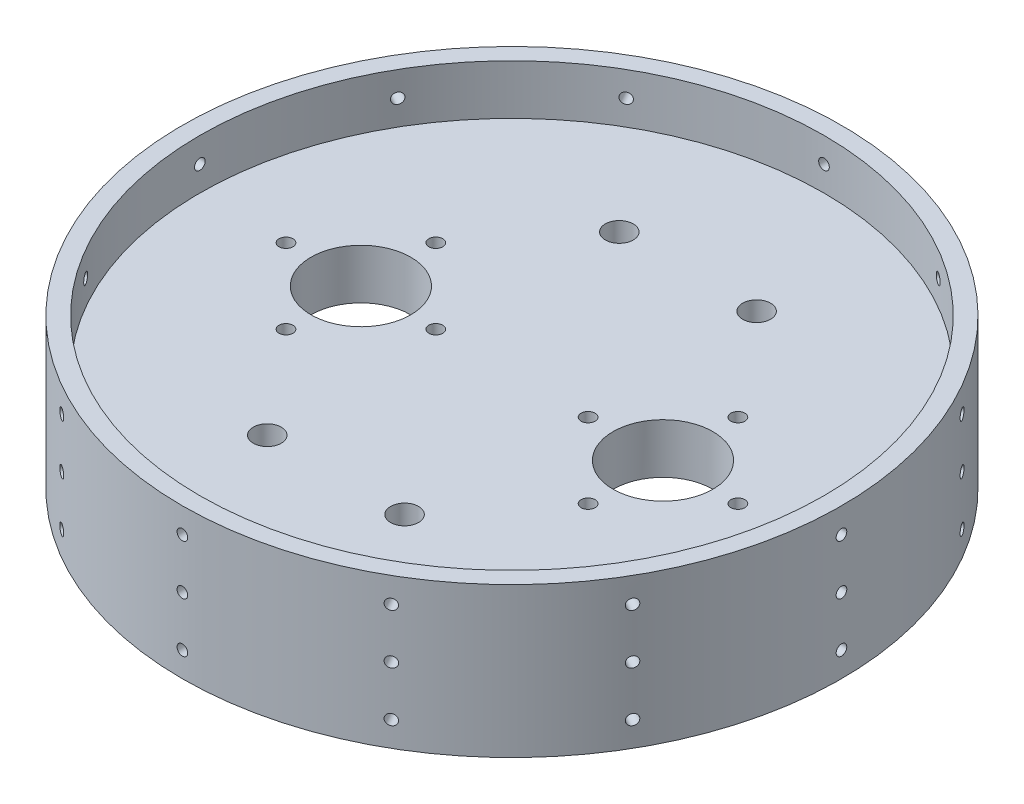
SolidWorks part; units mm, degrees
material "6061-T6 (SS)"
ref_plane "Front" through (0, 0, 0) normal (0, 0, 1) x (1, 0, 0)
ref_plane "Top" through (0, 0, 0) normal (0, 1, 0) x (1, 0, 0)
ref_plane "Right" through (0, 0, 0) normal (1, 0, 0) x (0, 0, -1)
sketch "Sketch1" plane through (0, 0, 0) normal (0, 1, 0) x (1, 0, 0)
  line L1 (0, 0) -> (127.635, 0)
  line L2 (0, 0) -> (0, 127.635)
  line L3 (0, 127.635) -> (127.635, 127.635)
  line L4 (127.635, 0) -> (127.635, 127.635)
  dimension "D1" = 127.635
  dimension "D2" = 127.635
extrude "Main Plate" add sketch "Sketch1" along normal blind 12.7
sketch "Sketch9" plane through (0, 12.7, 0) normal (0, 1, 0) x (1, 0, 0)
  circle A0 centre (63.8175, 63.8175) radius 85.725
  dimension "D1" = 171.45
extrude "Boss-Extrude1" add sketch "Sketch9" against normal up to surface (12.7 mm away) contours A0 up to face at (63.8175, 0, -63.8175)
sketch "Sketch10" plane through (0, 12.7, 0) normal (0, 1, 0) x (1, 0, 0)
  circle A0 centre (63.8175, 63.8175) radius 97.0396
  circle A1 centre (63.8175, 63.8175) radius 83.82
extrude "Cut-Extrude1" cut sketch "Sketch10" against normal blind 167.64 contours A0 | A1
sketch "Sketch14" plane through (0, 12.7, 0) normal (0, 1, 0) x (1, 0, 0)
  line L0 (201.1692, 63.8175) -> (-73.4523, 63.8175) construction
ref_plane "Plane1" through (0, 0, -63.8175) normal (0, 0, -1) x (-1, 0, 0)
ref_plane "Plane3" through (0, 6.35, 0) normal (0, 1, 0) x (1, 0, 0)
ref_plane "Plane2" through (-20.0025, 0, 0) normal (-1, 0, 0) x (0, 0, 1)
sketch "Sketch18" plane through (0, 6.35, 0) normal (0, 1, 0) x (1, 0, 0)
  circle A0 centre (63.8175, 63.8175) radius 83.82
  circle A1 centre (63.8175, 63.8175) radius 79.375
  dimension "D1" = 158.75
extrude "Boss-Extrude2" add sketch "Sketch18" along normal mid plane 38.1
sketch "Sketch15" plane through (-20.0025, 0, 0) normal (-1, 0, 0) x (0, 0, 1)
  line L0 (-63.8175, 92.202) -> (-63.8175, -92.202) construction
  line L1 (20.0025, 12.7) -> (-147.6375, 12.7) construction
  line L2 (-147.6375, -12.7) -> (20.0025, -12.7) construction
  line L3 (15.5575, 25.4) -> (-143.1925, 25.4) construction
  circle A0 centre (-63.8175, 6.35) radius 1.3526
  circle A1 centre (-63.8175, 19.05) radius 1.3525
  circle A2 centre (-63.8175, -6.35) radius 1.3526
  dimension "D1" = 2.7051
  dimension "D2" = 6.35
  dimension "D3" = 2.7051
  dimension "D4" = 2.7051
  dimension "D5" = 6.35
  dimension "D6" = 6.35
extrude "Cut-Extrude3" cut sketch "Sketch15" against normal blind 15.24
pattern_circular "CirPattern1" count 12 over 360 about axis through (63.8175, 0, -63.8175) along (0, 1, 0) of "Cut-Extrude3"
sketch "Sketch20" plane through (0, 12.7, 0) normal (0, 1, 0) x (1, 0, 0)
  line L0 (63.8175, 143.1925) -> (63.8175, -15.5575) construction
  line L1 (-15.5575, 63.8175) -> (143.1925, 63.8175) construction
  circle A0 centre (63.8175, 63.8175) radius 79.375 construction
ref_plane "Plane4" through (63.8175, 0, 0) normal (-1, 0, 0) x (0, 0, 1)
sketch "Sketch21" plane through (0, 12.7, 0) normal (0, 1, 0) x (1, 0, 0)
  line L1 (-15.5575, 63.8175) -> (143.1925, 63.8175) construction
  line L2 (102.235, 63.8175) -> (102.235, 100.651) construction
  line L3 (63.8175, 87.3125) -> (63.8175, -87.3125) construction
  circle A0 centre (102.235, 63.8175) radius 12.7
  circle A1 centre (102.235, 82.8675) radius 1.778
  circle A2 centre (25.4, 63.8175) radius 12.7
  circle A3 centre (121.285, 63.8175) radius 1.778
  circle A4 centre (102.235, 44.7675) radius 1.778
  circle A5 centre (83.185, 63.8175) radius 1.778
  circle A6 centre (25.4, 82.8675) radius 1.778
  circle A7 centre (6.35, 63.8175) radius 1.778
  circle A8 centre (25.4, 44.7675) radius 1.778
  circle A9 centre (44.45, 63.8175) radius 1.778
  point P11 (0, 0)
  point P12 (0, 0)
  point P13 (0, 0)
  dimension "D1" = 25.4
  dimension "D2" = 3.556
  dimension "D6" = 19.05
  dimension "D3" = 19.05
  dimension "D4" = 76.835
  dimension "D7" = 19.05
  dimension "D5" = 4
extrude "CO2 Mounts" cut sketch "Sketch21" against normal through all
sketch "Sketch22" plane through (0, 12.7, 0) normal (0, 1, 0) x (1, 0, 0)
  line L0 (63.8175, 87.3125) -> (63.8175, -87.3125) construction
  line L1 (87.3125, 63.8175) -> (-87.3125, 63.8175) construction
  circle A0 centre (46.355, 108.585) radius 3.556
  circle A1 centre (81.28, 108.585) radius 3.556
  circle A2 centre (81.28, 19.05) radius 3.556
  circle A3 centre (46.355, 19.05) radius 3.556
  dimension "D1" = 7.112
  dimension "D2" = 34.925
  dimension "D3" = 89.535
extrude "Cut-Extrude5" cut sketch "Sketch22" against normal through all
